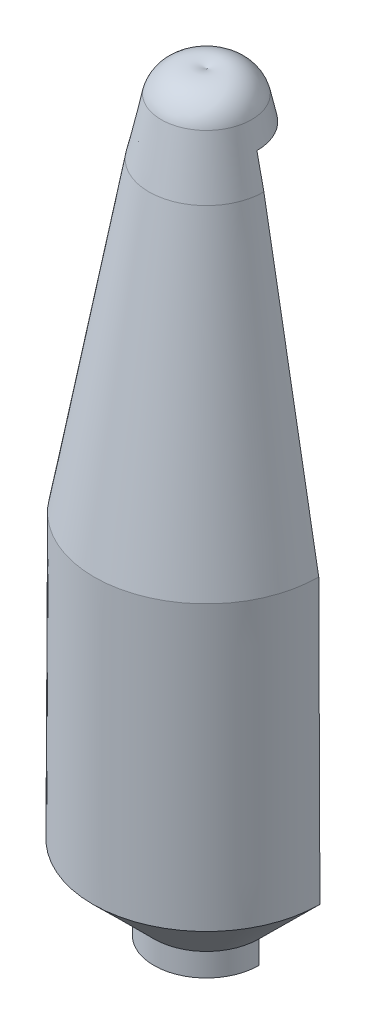
SolidWorks part; units mm, degrees
ref_plane "Front Plane" through (0, 0, 0) normal (0, 0, 1) x (1, 0, 0)
ref_plane "Top Plane" through (0, 0, 0) normal (0, 1, 0) x (1, 0, 0)
ref_plane "Right Plane" through (0, 0, 0) normal (1, 0, 0) x (0, 0, -1)
sketch "Sketch1" plane through (0, 0, 0) normal (1, 0, 0) x (0, 0, -1)
  line L0 (889, 5386.324) -> (1854.2, 0.0003)
  line L1 (1854.2, 0.0003) -> (1854.2, -914.3997)
  line L2 (1854.2, -914.3997) -> (1875.028, -914.3997)
  line L3 (1875.028, -914.3997) -> (1875.028, -4925.0597)
  line L4 (1875.028, -4925.0597) -> (797.687, -5991.8597)
  line L5 (797.687, -5991.8597) -> (797.687, -6450.5856)
  line L6 (1014.0088, 5408.7249) -> (1981.2, 11.2892)
  line L7 (1981.2, 11.2892) -> (2002.028, -4978.031)
  line L8 (889, 5386.324) -> (0, 5386.324)
  line L9 (0, 5386.324) -> (0, 6783.324)
  line L10 (2002.028, -4978.031) -> (924.687, -6044.831)
  line L11 (924.687, -6044.831) -> (924.687, -6450.5856)
  line L12 (1981.2, 11.2892) -> (1981.2, -787.3997) construction
  line L13 (1981.2, -787.3997) -> (2002.028, -787.3997) construction
  line L14 (2002.028, -787.3997) -> (2002.028, -4978.031) construction
  line L15 (797.687, -6450.5856) -> (924.687, -6450.5856)
  line L16 (1014.0088, 5408.7249) -> (797.687, 6403.5052)
  line L17 (0, 0) -> (0, 1746.8145) construction
  arc A0 (0, 6783.324) -> (797.687, 6403.5052) centre (236.0374, 6251.4928) cw
  dimension "D1" = 914.4
  dimension "D2" = 1854.2
  dimension "D3" = 889
  dimension "D4" = 5386.324
  dimension "D5" = 1875.028
  dimension "D6" = 4010.66
  dimension "D7" = 1066.8
  dimension "D8" = 797.687
  dimension "D10" = 1397
  dimension "D9" = 127
revolve "Revolve1" add sketch "Sketch1" angle 360 about L17
sketch "Sketch4" plane through (0, 0, 0) normal (1, 0, 0) x (0, 0, -1)
  line L1 (0, 5977.1357) -> (4011.0709, 5977.1357)
  line L2 (0, 5977.1357) -> (0, -7037.2023)
  line L3 (0, -7037.2023) -> (4011.0709, -7037.2023)
  line L4 (4011.0709, 5977.1357) -> (4011.0709, -7037.2023)
extrude "Extrude1" cut sketch "Sketch4" against normal mid plane 5080
